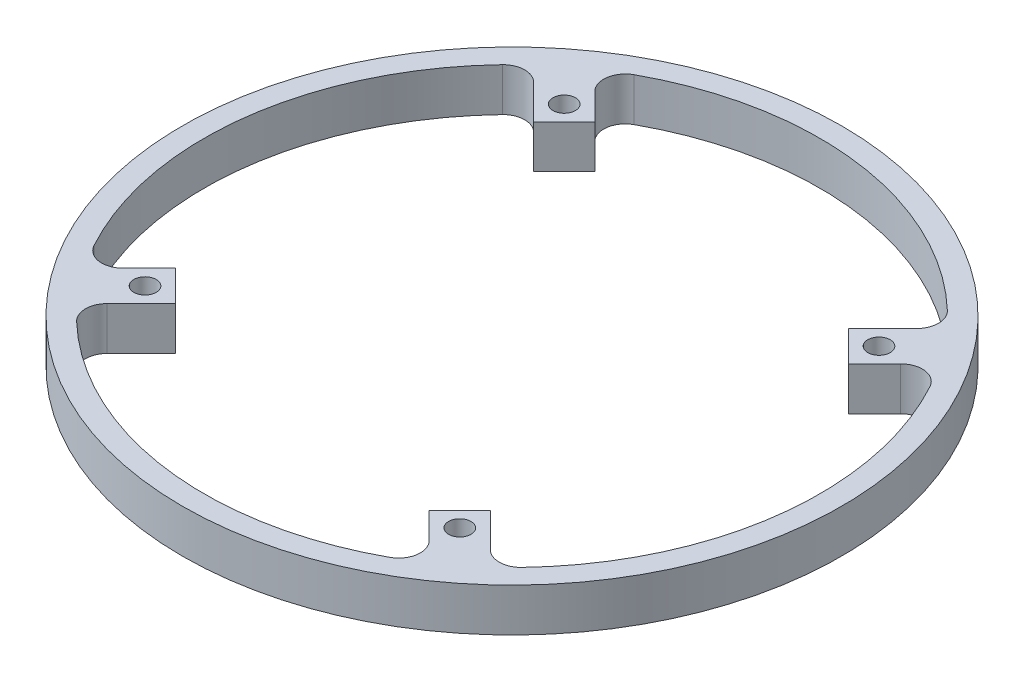
SolidWorks part; units mm, degrees
material "6061-T6 (SS)"
ref_plane "Front Plane" through (0, 0, 0) normal (0, 0, 1) x (1, 0, 0)
ref_plane "Top Plane" through (0, 0, 0) normal (0, 1, 0) x (1, 0, 0)
ref_plane "Right Plane" through (0, 0, 0) normal (1, 0, 0) x (0, 0, -1)
sketch "Sketch2" plane through (0, 0, 0) normal (1, 0, 0) x (0, 0, -1)
  line L0 (-55, 0) -> (-76.2, 0)
  line L1 (-76.2, 0) -> (-76.2, 10)
  line L2 (-76.2, 10) -> (-55, 10)
  line L5 (-55, 10) -> (-55, 0)
  dimension "D1" = 76.2
  dimension "D2" = 10
  dimension "D3" = 55
ref_axis "Axis1" through (0, 3.6789, 0) along (0, 1, 0)
revolve "Revolve1" add sketch "Sketch2" angle 360 about axis through (0, 3.6789, 0) along (0, 1, 0)
sketch "Sketch9" plane through (0, 0, 0) normal (0, 1, 0) x (1, 0, 0)
  line L1 (42.4264, -42.4264) -> (-42.4264, -42.4264) construction
  line L2 (42.4264, -42.4264) -> (42.4264, 42.4264) construction
  line L3 (42.4264, 42.4264) -> (-42.4264, 42.4264) construction
  line L4 (-42.4264, -42.4264) -> (-42.4264, 42.4264) construction
  line L5 (0, 0) -> (0, 27.9091) construction
  line L7 (0, 0) -> (26.5726, 0) construction
  line L11 (-43.4619, 48.4619) -> (-36.3909, 55.533) construction
  line L12 (-43.4619, 48.4619) -> (-36.3909, 41.3909) construction
  line L13 (-36.3909, 55.533) -> (-29.3198, 48.4619) construction
  line L16 (-36.3909, 41.3909) -> (-36.3909, 55.533) construction
  line L18 (-43.4619, 48.4619) -> (-29.3198, 48.4619) construction
  line L20 (-29.3198, 48.4619) -> (-36.3909, 41.3909) construction
  point P3 (-42.4264, 42.4264)
  point P355 (-36.3909, 48.4619)
  dimension "D1" = 1.0355
  dimension "D2" = 60
  dimension "D3" = 6.0355
  dimension "D4" = 6.1237
hole_wizard "#6 (0.204) Diameter Hole1" positions "Sketch12" profile "Sketch13" hole size "#6" standard "ANSI Inch" end condition through all
sketch "Sketch12" plane through (0, 0, 0) normal (0, -1, 0) x (-1, 0, 0)
  point P0 (36.3909, 48.4619)
sketch "Sketch13" plane through (-36.3909, 0, -48.4619) normal (1, 0, 0) x (0, 0, -1)
  line L0 (0, 0) -> (0, 10)
  line L1 (0, 10) -> (2.5908, 10)
  line L2 (2.5908, 10) -> (2.5908, 0)
  line L5 (2.5908, 0) -> (0, 0)
  line L11 (0, -6.35) -> (0, 107.95) construction
  dimension "Thru Hole Dia." = 5.1816
  dimension "Thru Hole Depth" = 10
sketch "Sketch14" plane through (0, 0, 0) normal (0, -1, 0) x (1, 0, 0)
  line L0 (0, 0) -> (-36.3909, -48.4619) construction
  line L1 (-33.0708, -38.0708) -> (-47.7839, -52.7839)
  line L2 (-58.9989, 39.8568) -> (-55.533, 36.3909)
  line L3 (0, 0) -> (-48.4619, 36.3909) construction
  line L4 (-43.4619, -48.4619) -> (-36.3909, -41.3909) construction
  line L5 (-55.533, 36.3909) -> (-48.4619, 29.3198)
  line L6 (-41.3909, 36.3909) -> (-48.4619, 29.3198) construction
  line L7 (-41.3909, 36.3909) -> (-48.4619, 43.4619) construction
  line L8 (-48.4619, 43.4619) -> (-55.533, 36.3909) construction
  line L9 (-48.4619, 29.3198) -> (-55.533, 36.3909) construction
  line L10 (-41.3909, 36.3909) -> (-55.533, 36.3909) construction
  line L11 (-48.4619, 43.4619) -> (-48.4619, 29.3198) construction
  line L12 (-48.4619, 29.3198) -> (-41.3909, 36.3909)
  line L13 (-43.4619, -48.4619) -> (-36.3909, -55.533) construction
  line L14 (0, 0) -> (26.5726, 0) construction
  line L15 (-41.3909, 36.3909) -> (-38.0708, 33.0708)
  arc A0 (-33.0708, -38.0708) -> (-38.0708, 33.0708) centre (0, 0) cw
  arc A1 (-58.9989, 39.8568) -> (-47.7839, -52.7839) centre (0, 0) ccw
  circle A2 centre (0, 0) radius 76.2 construction
  point P14 (-48.4619, 36.3909)
  dimension "D2" = 5
  dimension "D3" = 50.4288
extrude "Cut-Extrude1" cut sketch "Sketch14" against normal through all
pattern_circular "CirPattern1" count 4 over 360 about axis through (0, 0, 0) along (0, 1, 0) of "Cut-Extrude1", "#6 (0.204) Diameter Hole1"
fillet "Fillet1" radius 5 8 edges at (47.7839, 5, 52.7839) (-47.7839, 5, -52.7839) (52.7839, 5, -47.7839) (-52.7839, 5, 47.7839) (39.8568, 5, 58.9989) (58.9989, 5, -39.8568) (-39.8568, 5, -58.9989) (-58.9989, 5, 39.8568)
equation "\"TubeDiameter\" = 6.000in"
equation "\"D1@Sketch2\"=\"TubeDiameter\"/2"
